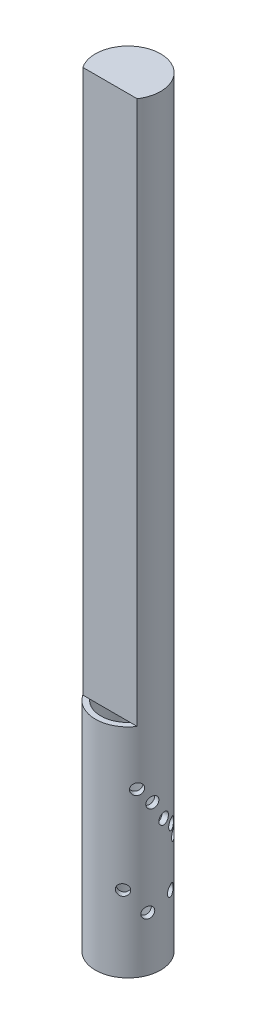
SolidWorks part; units mm, degrees
ref_plane "Front" through (0, 0, 0) normal (0, 0, 1) x (1, 0, 0)
ref_plane "Top" through (0, 0, 0) normal (0, 1, 0) x (1, 0, 0)
ref_plane "Right" through (0, 0, 0) normal (1, 0, 0) x (0, 0, -1)
sketch "Sketch1" plane through (0, 0, 0) normal (0, 1, 0) x (1, 0, 0)
  circle A0 centre (0, 0) radius 12.5
  circle A1 centre (0, 0) radius 15
  dimension "D1" = 25
  dimension "D2" = 30
extrude "Boss-Extrude1" add sketch "Sketch1" along normal blind 100
sketch "Sketch5" plane through (0, 100, 0) normal (0, 1, 0) x (1, 0, 0)
  line L0 (-12.5, -8.2916) -> (12.5, -8.2916)
  arc A0 (12.5, -8.2916) -> (-12.5, -8.2916) centre (0, 0) ccw
  dimension "D2" = 25
  dimension "D1" = 30
extrude "Boss-Extrude2" add sketch "Sketch5" along normal blind 250
hole_wizard "#8 (0.199) Diameter Hole1" positions "3DSketch1" profile "Sketch3" hole size "#8" standard "ANSI Inch"
sketch3d "3DSketch1"
  circle A0 centre (0, 0, 0) radius 15 construction
  point P0 (13.7396, 28.3202, -6.0185)
  point P2 (-9.3762, 34.9727, -11.7084)
  point P4 (12.2132, 48.59, -8.7084)
  point P6 (13.4163, 54.378, -6.7084)
  point P8 (14.9024, 59.6256, -1.7084)
  point P17 (14.6344, 68.3362, 3.2916)
  point P19 (12.5, 75, 8.2916)
  point P22 (-14.1635, 25, -4.9391)
  point P23 (-8.4772, 0, 12.3748)
  point P27 (0, 15, 0)
  point P28 (12.5, 75, 8.2916)
  dimension "D1" = 25
  dimension "D3" = 0
  dimension "D2" = 25
  dimension "D4" = 5
  dimension "D5" = 10
  dimension "D6" = 15
  dimension "D7" = 17
  dimension "D8" = 20
sketch "Sketch3" plane through (13.7396, 28.3202, -6.0185) normal (0, 1, 0) x (-0.4012, 0, -0.916)
  line L0 (0, 0) -> (0, 34.7581)
  line L1 (0, 34.7581) -> (2.5273, 34.7581)
  line L2 (2.5273, 34.7581) -> (2.5273, 0)
  line L5 (2.5273, 0) -> (0, 0)
  line L11 (0, -6.35) -> (0, 107.95) construction
  dimension "Thru Hole Dia." = 5.0546
  dimension "Thru Hole Depth" = 34.7581
